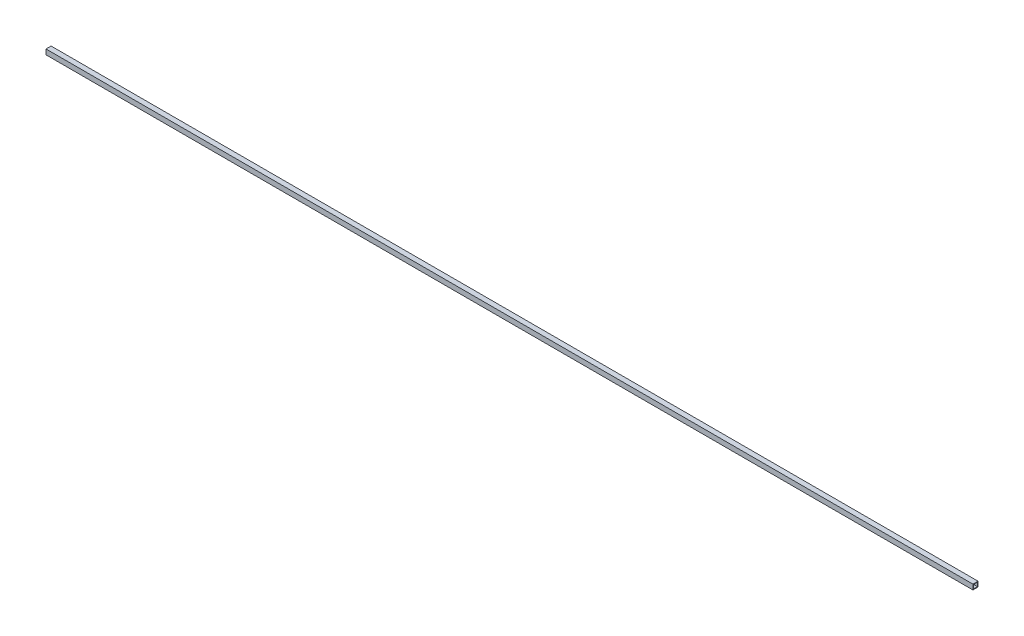
SolidWorks part; units mm, degrees
material "AISI 304"
ref_plane "Plan de face" through (0, 0, 0) normal (0, 0, 1) x (1, 0, 0)
ref_plane "Plan de dessus" through (0, 0, 0) normal (0, 1, 0) x (1, 0, 0)
ref_plane "Plan de droite" through (0, 0, 0) normal (1, 0, 0) x (0, 0, -1)
sketch "Sketch1" plane through (0, 0, 0) normal (0, 0, 1) x (1, 0, 0)
  line L0 (0, 0) -> (9244.33, 0)
  dimension "D1" = 9244.33
other "Al tube square AL TUBE 2 SQR X 0.25 WALL(1)"
ref_plane "Plane1" through (0, 0, 0) normal (1, 0, 0) x (0, 1, 0)
sketch "Sketch11" plane through (0, 0, 0) normal (1, 0, 0) x (0, 1, 0)
  line L0 (-19.05, -19.05) -> (-19.05, 19.05)
  line L1 (19.05, 19.05) -> (-19.05, 19.05)
  line L2 (19.05, 19.05) -> (19.05, -19.05)
  line L3 (-19.05, -19.05) -> (19.05, -19.05)
  line L4 (-25.4, -25.4) -> (25.4, -25.4)
  line L5 (-25.4, -25.4) -> (-25.4, 25.4)
  line L6 (25.4, 25.4) -> (-25.4, 25.4)
  line L7 (25.4, 25.4) -> (25.4, -25.4)
  line L8 (0, -19.05) -> (0, -25.4) construction
  line L9 (0, -19.05) -> (0, 19.05) construction
  line L10 (0, 19.05) -> (0, 25.4) construction
  line L11 (25.4, 0) -> (19.05, 0) construction
  line L12 (19.05, 0) -> (-19.05, 0) construction
  line L13 (-19.05, 0) -> (-25.4, 0) construction
  point P14 (0, 0)
  point P17 (0, 0)
  dimension "Thickness" = 6.35
  dimension "V_leg" = 50.8
  dimension "H_leg" = 50.8
